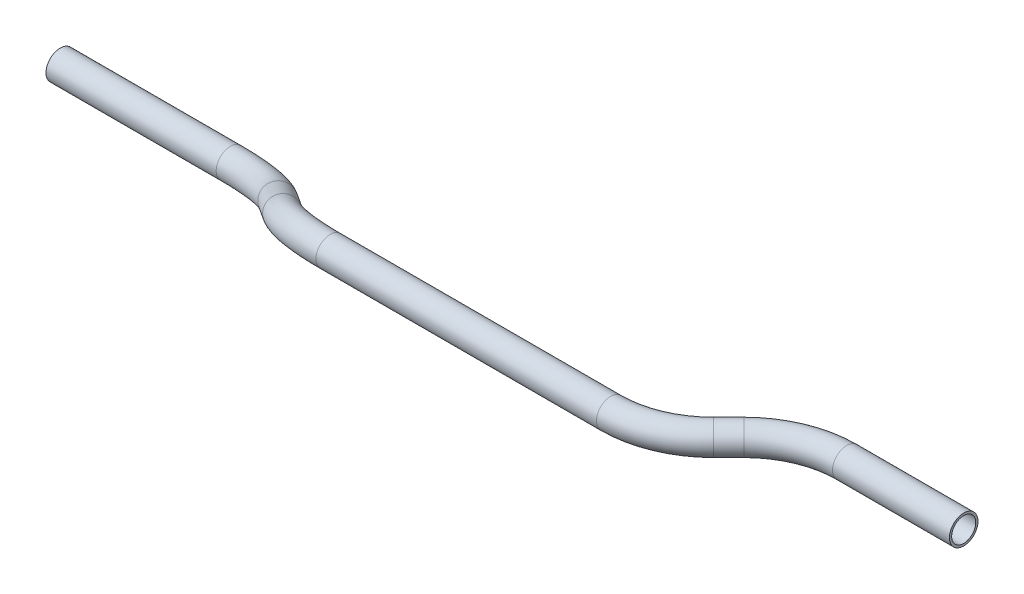
SolidWorks part; units mm, degrees
ref_plane "Front Plane" through (0, 0, 0) normal (0, 0, 1) x (1, 0, 0)
ref_plane "Top Plane" through (0, 0, 0) normal (0, 1, 0) x (1, 0, 0)
ref_plane "Right Plane" through (0, 0, 0) normal (1, 0, 0) x (0, 0, -1)
sketch3d "3DSketch2"
  line L0 (0, 0, 0) -> (94.5664, 0, 0)
  line L1 (0, 27.2535, 0) -> (0, 27.2535, 41.91) construction
  line L2 (0, 27.2535, 41.91) -> (467.4369, 27.2535, 41.91) construction
  line L3 (134.9775, 9.1253, 14.0327) -> (151.4918, 18.1282, 27.8773)
  line L4 (437.013, 27.2535, 0) -> (501.9942, 27.2535, 0)
  line L5 (0, 0, 0) -> (0, 27.2535, 0) construction
  line L6 (0, 27.2535, 0) -> (467.4369, 27.2535, 0) construction
  line L7 (191.903, 27.2535, 41.91) -> (347.7584, 27.2535, 41.91)
  line L8 (388.1695, 27.2535, 25.1712) -> (396.6018, 27.2535, 16.7388)
  arc A0 (396.6018, 27.2535, 16.7388) -> (437.013, 27.2535, 0) centre (437.013, 27.2535, 57.15) ccw
  arc A1 (347.7584, 27.2535, 41.91) -> (388.1695, 27.2535, 25.1712) centre (347.7584, 27.2535, -15.24) ccw
  arc A2 (151.4918, 18.1282, 27.8773) -> (191.903, 27.2535, 41.91) centre (191.903, -3.9022, -6.0008) ccw
  arc A3 (94.5664, 0, 0) -> (134.9775, 9.1253, 14.0327) centre (94.5664, 31.1558, 47.9108) ccw
  point P7 (413.3407, 27.2535, 0)
  point P9 (437.013, -29.8965, 57.15)
  point P12 (371.4307, 27.2535, 41.91)
  point P14 (347.7584, 84.4035, -15.24)
  point P17 (168.2307, 27.2535, 41.91)
  point P19 (191.903, 44.0085, -37.1565)
  point P22 (118.2387, 0, 0)
  point P26 (94.5664, -16.755, 79.0665)
  dimension "D5" = 203.2
  dimension "D10" = 27.2535
  dimension "D7" = 57.15
  dimension "D1" = 118.2387
  dimension "D2" = 41.91
  dimension "D3" = 45
  dimension "D4" = 135
  dimension "D6" = 88.6535
  dimension "D11" = 467.4369
ref_plane "Plane1" through (0, 0, 0) normal (1, 0, 0) x (0, 0, -1)
sketch "Sketch1" plane through (0, 0, 0) normal (1, 0, 0) x (0, 0, -1)
  circle A0 centre (0, 0) radius 7.9375
  circle A1 centre (0, 0) radius 6.6929
  dimension "D1" = 15.875
  dimension "D2" = 1.2446
sweep "Sweep2" add profiles "Sketch1" path "3DSketch2"
